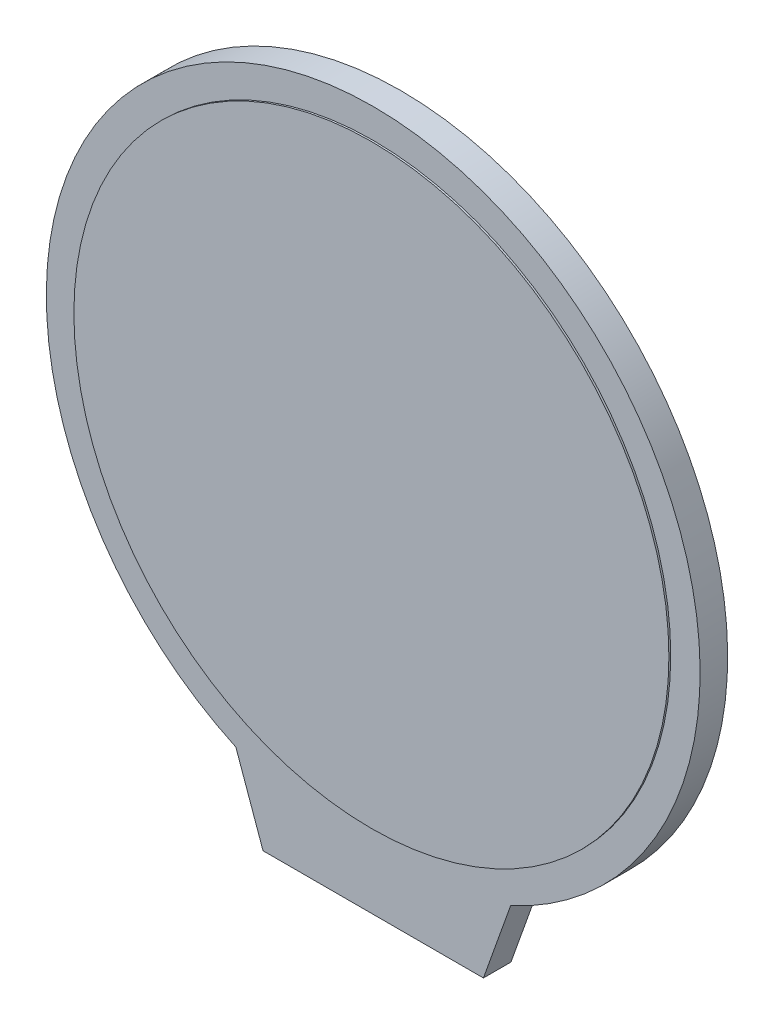
SolidWorks part; units mm, degrees
ref_plane "前视基准面" through (0, 0, 0) normal (0, 0, 1) x (1, 0, 0)
ref_plane "上视基准面" through (0, 0, 0) normal (0, 1, 0) x (1, 0, 0)
ref_plane "右视基准面" through (0, 0, 0) normal (1, 0, 0) x (0, 0, -1)
sketch "草图2" plane through (0, 0, 0) normal (0, 0, 1) x (1, 0, 0)
  line L1 (-6, -20.3) -> (6, -20.3)
  line L2 (6, -20.3) -> (7.4798, -16.1522)
  line L3 (-6, -20.3) -> (-7.4798, -16.1522)
  arc A0 (7.4798, -16.1522) -> (-7.4798, -16.1522) centre (0, 0) ccw
extrude "凸台-拉伸1" add sketch "草图2" along normal blind 1.5
sketch "草图3" plane through (0, 0, 1.5) normal (0, 0, 1) x (1, 0, 0)
  circle A0 centre (0, 0) radius 16.2
extrude "凸台-拉伸2" add sketch "草图3" along normal blind 0.1
